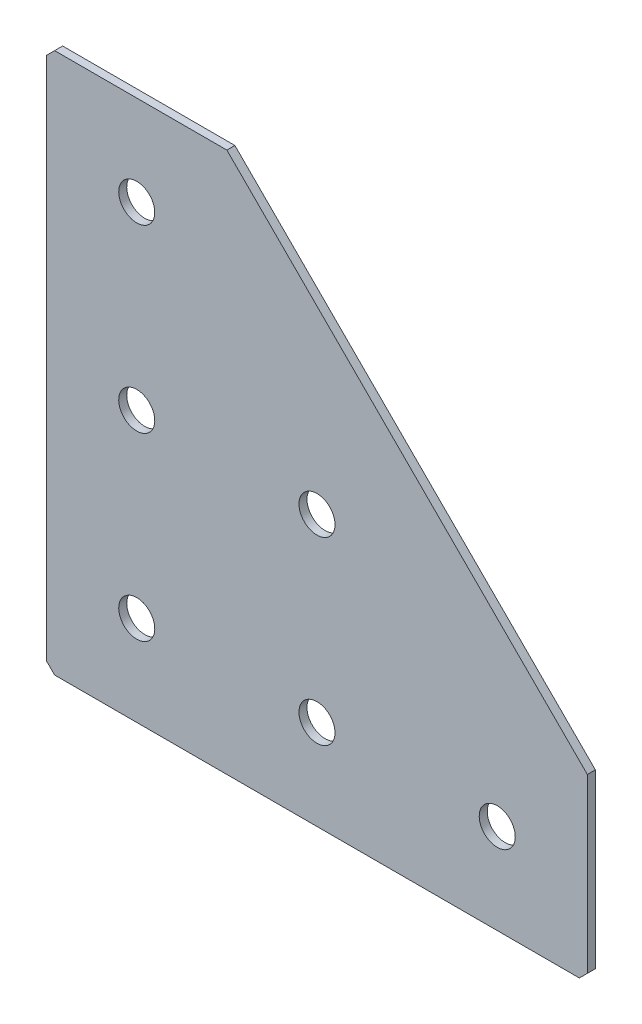
SolidWorks part; units mm, degrees
material "Простая углеродистая сталь"
ref_plane "Спереди(Плоскость XY)" through (0, 0, 0) normal (0, 0, 1) x (1, 0, 0)
ref_plane "Сверху(Плоскость XZ)" through (0, 0, 0) normal (0, 1, 0) x (1, 0, 0)
ref_plane "Справа(Плоскость ZY)" through (0, 0, 0) normal (1, 0, 0) x (0, 0, -1)
sketch "Эскиз1" plane through (0, 0, 0) normal (0, 0, -1) x (1, 0, 0)
  line L0 (0, 0) -> (0, 135)
  line L1 (0, 135) -> (135, 135)
  line L2 (135, 135) -> (135, 90)
  line L3 (135, 90) -> (45, 90) construction
  line L4 (45, 90) -> (45, 0) construction
  line L5 (45, 0) -> (0, 0)
  line L6 (135, 90) -> (45, 0)
  dimension "D1" = 135
  dimension "D3" = 45
extrude "Бобышка-Вытянуть1" add sketch "Эскиз1" along normal blind 2
hole_wizard "Отверстие с зазором M81" positions "Эскиз2" profile "Эскиз3" hole size "M8" standard "DIN" end condition through all
sketch "Эскиз2" plane through (0, 0, -2) normal (0, 0, -1) x (1, 0, 0)
  line L0 (22.5, 0) -> (22.5, 112.5) construction
  line L1 (0, 0) -> (45, 0) construction
  line L3 (135, 112.5) -> (0, 112.5) construction
  line L5 (0, 135) -> (0, 0) construction
  line L6 (135, 90) -> (135, 135) construction
  point P0 (67.5, 112.5)
  point P2 (22.5, 112.5)
  point P4 (22.5, 67.5)
  point P6 (22.5, 22.5)
  point P21 (112.5, 112.5)
  point P30 (67.5, 67.5)
  dimension "D1" = 45
  dimension "D2" = 45
  dimension "D3" = 45
  dimension "D4" = 22.5
  dimension "D5" = 45
sketch "Эскиз3" plane through (67.5, -112.5, -2) normal (1, 0, 0) x (0, 1, 0)
  line L0 (0, 0) -> (0, 2)
  line L1 (0, 2) -> (4.5, 2)
  line L2 (4.5, 2) -> (4.5, 0)
  line L5 (4.5, 0) -> (0, 0)
  line L11 (0, -6.35) -> (0, 107.95) construction
  dimension "Диаметр сквозного отверстия" = 9
  dimension "Глубина сквозного отверстия" = 2
chamfer "Фаска1" distance 2 angle 45 3 edges at (0, 0, -1) (135, -135, -1) (0, -135, -1)
